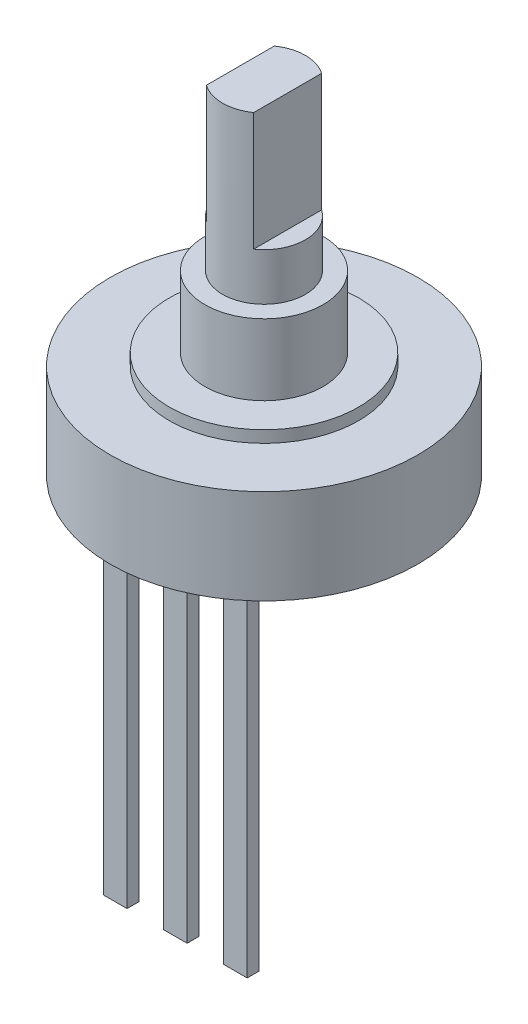
SolidWorks part; units mm, degrees
ref_plane "Front Plane" through (0, 0, 0) normal (0, 0, 1) x (1, 0, 0)
ref_plane "Top Plane" through (0, 0, 0) normal (0, 1, 0) x (1, 0, 0)
ref_plane "Right Plane" through (0, 0, 0) normal (1, 0, 0) x (0, 0, -1)
sketch "Sketch1" plane through (0, 0, 0) normal (0, 1, 0) x (1, 0, 0)
  circle A0 centre (0, 0) radius 1.75
  dimension "D1" = 3.5
extrude "Extrude1" add sketch "Sketch1" along normal blind 7
sketch "Sketch2" plane through (0, 7, 0) normal (0, 1, 0) x (1, 0, 0)
  line L0 (-1, 0) -> (1, 0) construction
  line L1 (-2.2906, 2.826) -> (-1, 2.826)
  line L2 (-2.2906, 2.826) -> (-2.2906, -1.8914)
  line L3 (-2.2906, -1.8914) -> (-1, -1.8914)
  line L4 (-1, 2.826) -> (-1, -1.8914)
  line L5 (2.4464, 2.5589) -> (1, 2.5589)
  line L6 (2.4464, 2.5589) -> (2.4464, -2.0472)
  line L7 (2.4464, -2.0472) -> (1, -2.0472)
  line L8 (1, 2.5589) -> (1, -2.0472)
  point P10 (0, 0)
  dimension "D1" = 2
extrude "Cut-Extrude1" cut sketch "Sketch2" against normal blind 5
sketch "Sketch3" plane through (0, 0, 0) normal (0, -1, 0) x (1, 0, 0)
  circle A0 centre (0, 0) radius 2.5
  dimension "D1" = 5
extrude "Extrude2" add sketch "Sketch3" along normal blind 3
sketch "Sketch4" plane through (0, -3, 0) normal (0, -1, 0) x (1, 0, 0)
  circle A0 centre (0, 0) radius 4
  dimension "D1" = 8
extrude "Extrude3" add sketch "Sketch4" along normal blind 0.5
sketch "Sketch5" plane through (0, -3.5, 0) normal (0, -1, 0) x (1, 0, 0)
  circle A0 centre (0, 0) radius 6.5
  dimension "D1" = 13
extrude "Extrude4" add sketch "Sketch5" along normal blind 4
sketch "Sketch7" plane through (0, -7.5, 0) normal (0, -1, 0) x (1, 0, 0)
  line L0 (-3.5683, 3.5) -> (5.4772, 3.5) construction
  line L1 (-2.04, 3.25) -> (-3.04, 3.75) construction
  line L2 (-0.5, 3.75) -> (0.5, 3.75)
  line L3 (-0.5, 3.75) -> (-0.5, 3.25)
  line L4 (-0.5, 3.25) -> (0.5, 3.25)
  line L5 (0.5, 3.75) -> (0.5, 3.25)
  line L6 (2.04, 3.75) -> (3.04, 3.75)
  line L7 (2.04, 3.75) -> (2.04, 3.25)
  line L8 (2.04, 3.25) -> (3.04, 3.25)
  line L9 (3.04, 3.75) -> (3.04, 3.25)
  line L10 (-2.04, 3.75) -> (-3.04, 3.75)
  line L11 (-2.04, 3.75) -> (-2.04, 3.25)
  line L12 (-2.04, 3.25) -> (-3.04, 3.25)
  line L13 (-3.04, 3.75) -> (-3.04, 3.25)
  line L14 (-0.5, 3.75) -> (0.5, 3.25) construction
  line L15 (3.04, 3.75) -> (2.04, 3.25) construction
  line L16 (-2.54, 3.5) -> (-2.54, 2.6269) construction
  line L17 (0, 3.5) -> (0, 1.819) construction
  line L18 (2.54, 3.5) -> (2.54, 2.4518) construction
  circle A0 centre (0, 0) radius 6.5 construction
  point P16 (2.54, 3.5)
  point P17 (0, 3.5)
  point P18 (-2.54, 3.5)
  dimension "D1" = 0.5
  dimension "D2" = 0.5
  dimension "D3" = 0.5
  dimension "D4" = 3.5
  dimension "D5" = 1
  dimension "D6" = 1
  dimension "D7" = 1
  dimension "D8" = 2.54
  dimension "D9" = 2.54
extrude "Extrude5" add sketch "Sketch7" along normal blind 15
